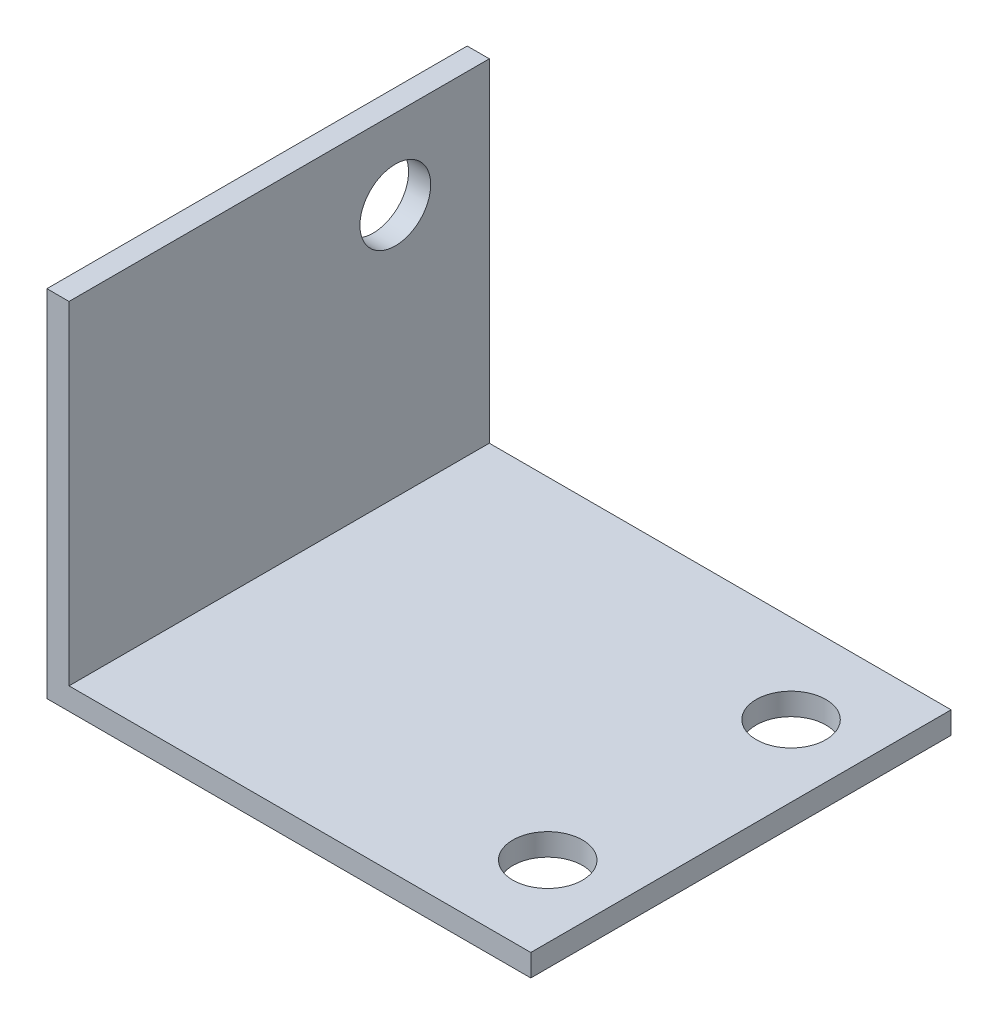
SolidWorks part; units mm, degrees
ref_plane "Front Plane" through (0, 0, 0) normal (0, 0, 1) x (1, 0, 0)
ref_plane "Top Plane" through (0, 0, 0) normal (0, 1, 0) x (1, 0, 0)
ref_plane "Right Plane" through (0, 0, 0) normal (1, 0, 0) x (0, 0, -1)
sketch "Sketch1" plane through (0, 0, 0) normal (0, 1, 0) x (1, 0, 0)
  line L0 (15.405, 11) -> (15.405, -11) construction
  line L1 (-21.875, 19) -> (21.875, 19)
  line L2 (-21.875, 19) -> (-21.875, -19)
  line L3 (-21.875, -19) -> (21.875, -19)
  line L4 (21.875, 19) -> (21.875, -19)
  line L5 (-21.875, 19) -> (21.875, -19) construction
  line L6 (-21.875, -19) -> (21.875, 19) construction
  circle A0 centre (15.405, 11) radius 3.15
  circle A1 centre (15.405, -11) radius 3.15
  point P0 (0, 0)
  dimension "D3" = 6.3
  dimension "D4" = 6.3
  dimension "D1" = 38
  dimension "D2" = 43.75
  dimension "D5" = 6.47
  dimension "D6" = 8
  dimension "D7" = 8
extrude "Base" add sketch "Sketch1" along normal blind 2
sketch "Sketch2" plane through (-21.875, 0, 0) normal (-1, 0, 0) x (0, 0, 1)
  line L1 (-19, 0) -> (19, 0)
  line L2 (-19, 0) -> (-19, 32.1)
  line L3 (-19, 32.1) -> (19, 32.1)
  line L4 (19, 0) -> (19, 32.1)
  circle A0 centre (-10.5, 24.9) radius 3.2
  dimension "D2" = 6.4
  dimension "D1" = 32.1
  dimension "D3" = 8.5
  dimension "D4" = 7.2
extrude "Tab" add sketch "Sketch2" against normal blind 2
